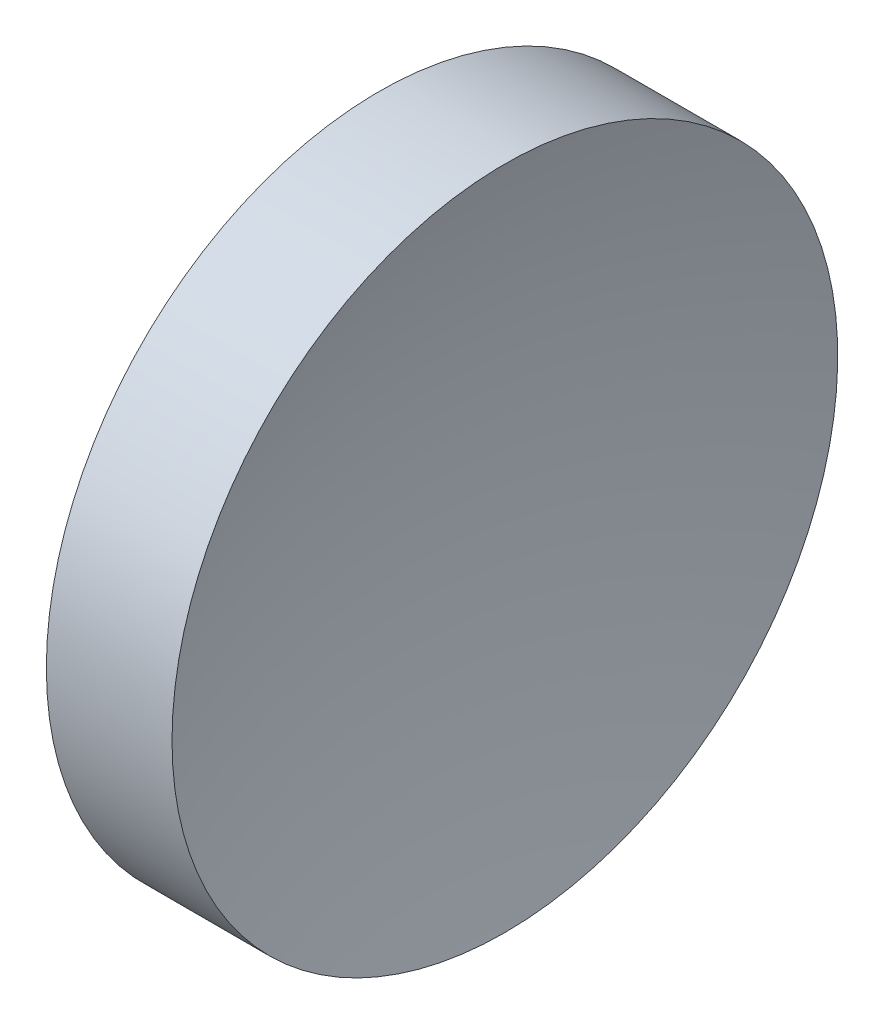
SolidWorks part; units mm, degrees
ref_plane "前视基准面" through (0, 0, 0) normal (0, 0, 1) x (1, 0, 0)
ref_plane "上视基准面" through (0, 0, 0) normal (0, 1, 0) x (1, 0, 0)
ref_plane "右视基准面" through (0, 0, 0) normal (1, 0, 0) x (0, 0, -1)
sketch "草图1" plane through (0, 0, 0) normal (0, 0, 1) x (1, 0, 0)
  line L0 (44.7821, 28.4776) -> (52.988, 28.4776) construction
  line L1 (47.7537, 28.4776) -> (47.7537, 34.8276)
  line L2 (47.7537, 34.8276) -> (50.1509, 34.8276)
  line L3 (49.2537, 28.4776) -> (47.7537, 28.4776)
  arc A0 (50.1509, 34.8276) -> (49.2537, 28.4776) centre (72.1737, 28.4776) ccw
revolve "旋转1" add sketch "草图1" angle 360 about L0
